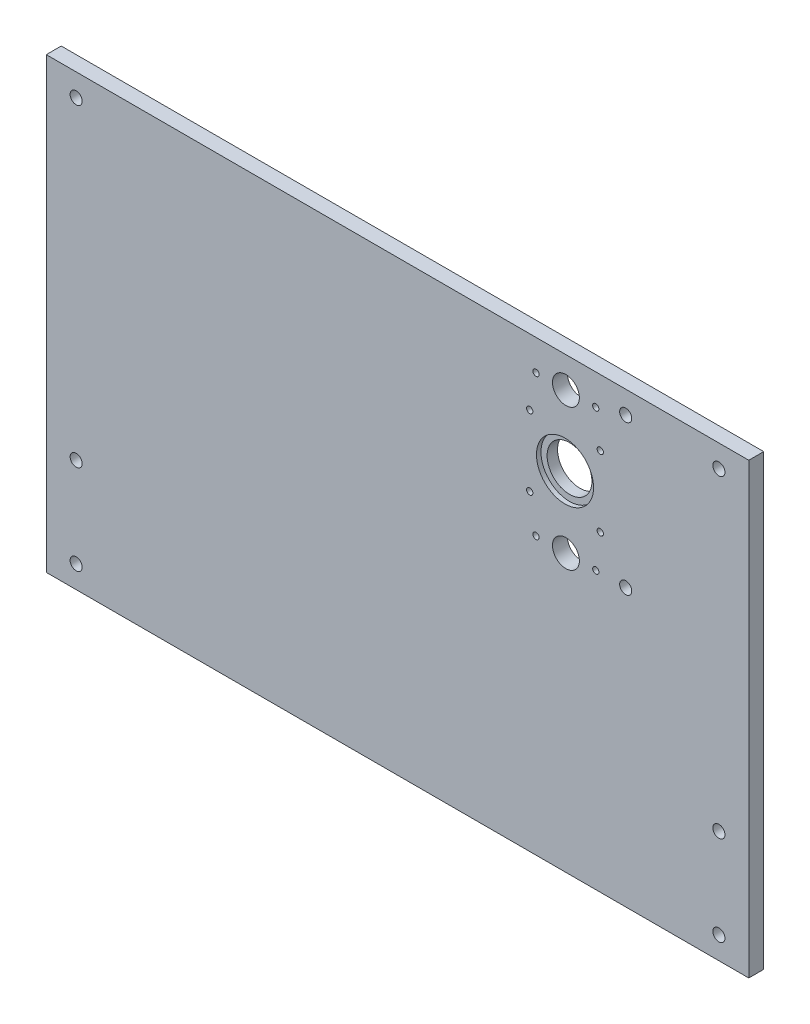
SolidWorks part; units mm, degrees
material "6061 Alloy"
ref_plane "Front Plane" through (0, 0, 0) normal (0, 0, 1) x (1, 0, 0)
ref_plane "Top Plane" through (0, 0, 0) normal (0, 1, 0) x (1, 0, 0)
ref_plane "Right Plane" through (0, 0, 0) normal (1, 0, 0) x (0, 0, -1)
sketch "Sketch2" plane through (0, 0, 0) normal (0, 0, 1) x (1, 0, 0)
  line L1 (-235, -150) -> (235, -150)
  line L2 (-235, -150) -> (-235, 150)
  line L3 (-235, 150) -> (235, 150)
  line L4 (235, -150) -> (235, 150)
  line L5 (-235, -150) -> (235, 150) construction
  line L6 (-235, 150) -> (235, -150) construction
  point P0 (0, 0)
  dimension "D1" = 470
  dimension "D2" = 300
extrude "Boss-Extrude1" add sketch "Sketch2" along normal mid plane 10
sketch "Sketch3" plane through (0, 0, 5) normal (0, 0, 1) x (1, 0, 0)
  line L0 (-215, -1058.5557) -> (-215, 48941.4443) construction
  line L1 (-235, 150) -> (-235, -150) construction
  line L2 (-1130.8828, -135) -> (48869.1172, -135) construction
  line L3 (-1138.1256, -75) -> (48861.8744, -75) construction
  line L4 (-235, -150) -> (235, -150) construction
  line L5 (215, -1025.1068) -> (215, 48974.8932) construction
  line L6 (235, -150) -> (235, 150) construction
  line L7 (-1174.5815, 135) -> (48825.4185, 135) construction
  line L8 (235, 150) -> (-235, 150) construction
  circle A0 centre (-215, -75) radius 4.05
  circle A1 centre (-215, -135) radius 4.05
  circle A2 centre (215, -75) radius 4.05
  circle A3 centre (215, -135) radius 4.05
  circle A4 centre (-215, 135) radius 4.05
  circle A5 centre (215, 135) radius 4.05
  dimension "D5" = 8.1
  dimension "D6" = 8.1
  dimension "D7" = 8.1
  dimension "D8" = 8.1
  dimension "D10" = 8.1
  dimension "D11" = 8.1
  dimension "D1" = 20
  dimension "D2" = 15
  dimension "D3" = 60
  dimension "D4" = 20
  dimension "D9" = 15
extrude "Cut-Extrude1" cut sketch "Sketch3" against normal blind 10
sketch "Sketch4" plane through (0, 0, 5) normal (0, 0, 1) x (1, 0, 0)
  line L0 (-1048.1305, 129.5) -> (48951.8695, 129.5) construction
  line L1 (-1078.5537, 35) -> (48921.4463, 35) construction
  line L2 (112.65, -948.1906) -> (112.65, 49051.8094) construction
  line L3 (-235, -150) -> (235, -150) construction
  line L4 (-235, 150) -> (-235, -150) construction
  circle A0 centre (112.65, 129.5) radius 9
  circle A1 centre (112.65, 35) radius 9
  circle A2 centre (92.65, 129.5) radius 2.1
  circle A3 centre (132.65, 129.5) radius 2.1
  circle A4 centre (132.65, 35) radius 2.1
  circle A5 centre (92.65, 35) radius 2.1
  dimension "D4" = 18
  dimension "D5" = 18
  dimension "D8" = 4.2
  dimension "D9" = 4.2
  dimension "D12" = 4.2
  dimension "D13" = 4.2
  dimension "D1" = 185
  dimension "D2" = 94.5
  dimension "D3" = 347.65
  dimension "D6" = 20
  dimension "D7" = 20
  dimension "D10" = 20
  dimension "D11" = 20
extrude "Cut-Extrude2" cut sketch "Sketch4" against normal through all
sketch "Sketch5" plane through (0, 0, 5) normal (0, 0, 1) x (1, 0, 0)
  line L0 (152.65, -981.5111) -> (152.65, 49018.4889) construction
  line L1 (-1025.0374, 135) -> (48974.9626, 135) construction
  line L2 (-1021.6922, 35) -> (48978.3078, 35) construction
  line L3 (235, 150) -> (-235, 150) construction
  circle A0 centre (112.65, 129.5) radius 9 construction
  circle A1 centre (152.65, 135) radius 4.05
  circle A2 centre (152.65, 35) radius 4.05
  dimension "D1" = 40
  dimension "D4" = 8.1
  dimension "D5" = 8.1
  dimension "D2" = 15
  dimension "D3" = 100
extrude "Cut-Extrude3" cut sketch "Sketch5" against normal through all
sketch "Sketch7" plane through (0, 0, 5) normal (0, 0, 1) x (1, 0, 0)
  circle A0 centre (112.05, 82.25) radius 19.1
  circle A1 centre (112.65, 129.5) radius 9 construction
  dimension "D1" = 38.2
  dimension "D2" = 0.6
  dimension "D3" = 47.25
extrude "Cut-Extrude5" cut sketch "Sketch7" against normal blind 3
sketch "Sketch8" plane through (0, 0, 2) normal (0, 0, 1) x (1, 0, 0)
  circle A0 centre (112.05, 82.25) radius 15
  dimension "D1" = 30
extrude "Cut-Extrude6" cut sketch "Sketch8" against normal through all
sketch "Sketch9" plane through (0, 0, 5) normal (0, 0, 1) x (1, 0, 0)
  line L1 (88.45, 58.65) -> (135.65, 58.65) construction
  line L2 (88.45, 58.65) -> (88.45, 105.85) construction
  line L3 (88.45, 105.85) -> (135.65, 105.85) construction
  line L4 (135.65, 58.65) -> (135.65, 105.85) construction
  line L5 (88.45, 58.65) -> (135.65, 105.85) construction
  line L6 (88.45, 105.85) -> (135.65, 58.65) construction
  circle A0 centre (88.45, 105.85) radius 2.1
  circle A1 centre (135.65, 105.85) radius 2.1
  circle A2 centre (135.65, 58.65) radius 2.1
  circle A3 centre (88.45, 58.65) radius 2.1
  point P0 (112.05, 82.25)
  dimension "D3" = 4.2
  dimension "D4" = 4.2
  dimension "D5" = 4.2
  dimension "D6" = 4.2
  dimension "D1" = 47.2
  dimension "D2" = 47.2
extrude "Cut-Extrude7" cut sketch "Sketch9" against normal through all
equation "\"D6@Sketch3\"=\"D5@Sketch3\""
equation "\"D7@Sketch3\"=\"D5@Sketch3\""
equation "\"D8@Sketch3\"=\"D5@Sketch3\""
equation "\"D5@Sketch4\"=\"D4@Sketch4\""
equation "\"D1@Sketch5\"=40"
equation "\"D4@Sketch9\"=\"D3@Sketch9\""
equation "\"D5@Sketch9\"=\"D3@Sketch9\""
equation "\"D6@Sketch9\"=\"D3@Sketch9\""
equation "\"D3@Sketch7\"=94.5/2"
equation "\"D10@Sketch3\"=\"D5@Sketch3\""
equation "\"D11@Sketch3\"=\"D5@Sketch3\""
